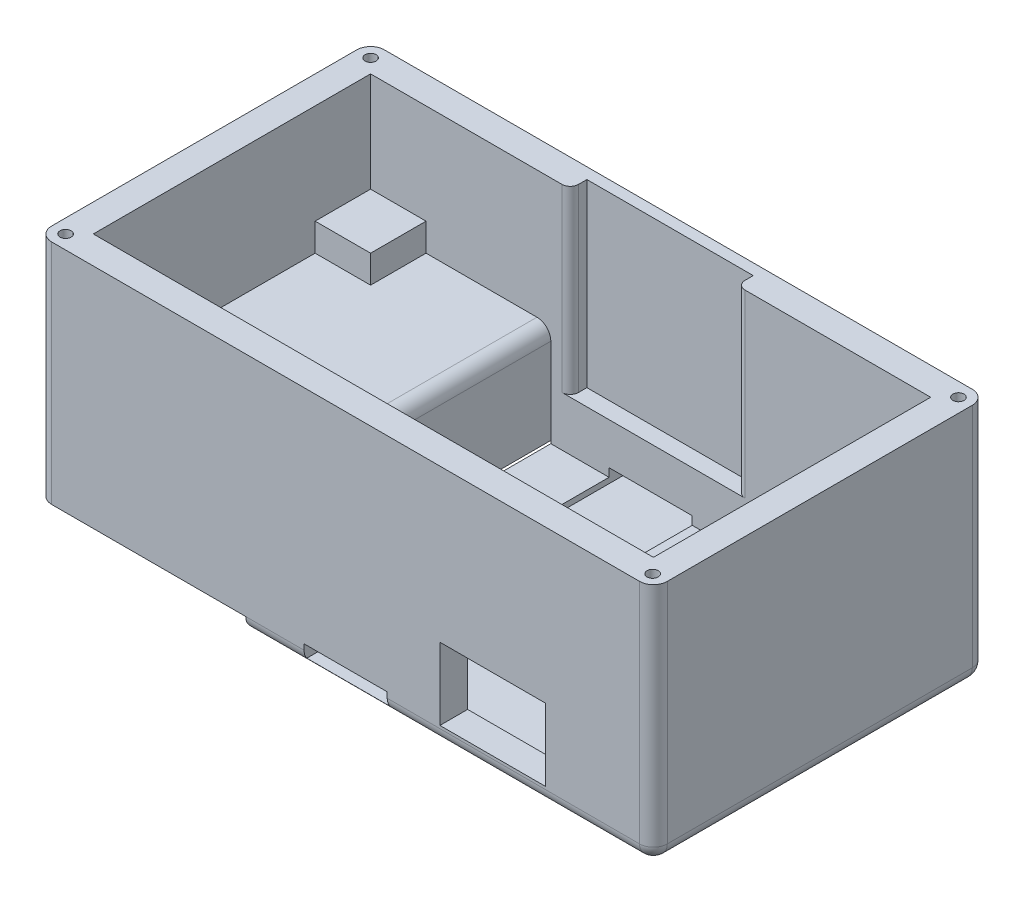
SolidWorks part; units mm, degrees
ref_plane "Front Plane" through (0, 0, 0) normal (0, 0, 1) x (1, 0, 0)
ref_plane "Top Plane" through (0, 0, 0) normal (0, 1, 0) x (1, 0, 0)
ref_plane "Right Plane" through (0, 0, 0) normal (1, 0, 0) x (0, 0, -1)
sketch "Sketch1" plane through (0, 0, 0) normal (0, 1, 0) x (1, 0, 0)
  line L1 (0, 0) -> (111, 0)
  line L2 (0, 0) -> (0, 60)
  line L3 (0, 60) -> (111, 60)
  line L4 (111, 0) -> (111, 60)
  dimension "D1" = 111
  dimension "D2" = 60
extrude "Boss-Extrude1" add sketch "Sketch1" along normal blind 43.5
sketch "Sketch2" plane through (0, 43.5, 0) normal (0, 1, 0) x (1, 0, 0)
  line L0 (55.5, 60) -> (55.5, 0) construction
  line L1 (111, 60) -> (0, 60) construction
  line L2 (0, 0) -> (111, 0) construction
  line L3 (0, 30) -> (111, 30) construction
  line L4 (0, 60) -> (0, 0) construction
  line L5 (111, 0) -> (111, 60) construction
  line L7 (5, 5) -> (106, 5)
  line L8 (5, 5) -> (5, 55)
  line L9 (5, 55) -> (106, 55)
  line L10 (106, 5) -> (106, 55)
  dimension "D1" = 5
  dimension "D2" = 5
  dimension "D3" = 5
  dimension "D4" = 5
  dimension "D5" = 50
  dimension "D6" = 101
extrude "Cut-Extrude1" cut sketch "Sketch2" against normal blind 18
sketch "Sketch3" plane through (0, 43.5, 0) normal (0, 1, 0) x (1, 0, 0)
  line L0 (5, 45) -> (15, 45)
  line L1 (5, 55) -> (5, 5) construction
  line L2 (15, 45) -> (15, 55)
  line L3 (106, 55) -> (5, 55) construction
  line L4 (15, 55) -> (96, 55)
  line L5 (96, 55) -> (96, 45)
  line L6 (96, 45) -> (106, 45)
  line L7 (106, 5) -> (106, 55) construction
  line L8 (106, 45) -> (106, 15)
  line L9 (106, 5) -> (106, 55) construction
  line L10 (106, 15) -> (96, 15)
  line L11 (96, 15) -> (96, 5)
  line L12 (5, 5) -> (106, 5) construction
  line L13 (96, 5) -> (15, 5)
  line L14 (15, 5) -> (15, 15)
  line L15 (15, 15) -> (5, 15)
  line L16 (5, 55) -> (5, 5) construction
  line L17 (5, 15) -> (5, 45)
  dimension "D1" = 10
  dimension "D2" = 10
  dimension "D3" = 10
  dimension "D4" = 10
  dimension "D5" = 10
  dimension "D6" = 10
  dimension "D7" = 10
  dimension "D8" = 10
extrude "Cut-Extrude3" cut sketch "Sketch3" against normal blind 23
sketch "Sketch5" plane through (0, 0, 0) normal (0, -1, 0) x (1, 0, 0)
  line L6 (0, 0) -> (111, 0) construction
  line L14 (111, 0) -> (111, -60) construction
  line L15 (106, -55) -> (37.5, -55)
  line L16 (106, -55) -> (106, -5)
  line L17 (106, -5) -> (37.5, -5)
  line L18 (37.5, -55) -> (37.5, -5)
  line L19 (111, -60) -> (0, -60) construction
  dimension "D6" = 5
  dimension "D7" = 5
  dimension "D8" = 5
extrude "Cut-Extrude5" cut sketch "Sketch5" against normal blind 18.5 from offset 2 offset against normal yes
sketch "Sketch6" plane through (0, 0, 0) normal (0, -1, 0) x (1, 0, 0)
  line L0 (0, 0) -> (111, 0) construction
  line L1 (0, -60) -> (37.5, -60)
  line L2 (0, -60) -> (0, 0)
  line L3 (0, 0) -> (37.5, 0)
  line L4 (37.5, -60) -> (37.5, 0)
  dimension "D1" = 60
  dimension "D2" = 37.5
extrude "Cut-Extrude6" cut sketch "Sketch6" against normal blind 2.5
sketch "Sketch7" plane through (0, 2.5, 0) normal (0, -1, 0) x (-1, 0, 0)
  line L0 (-37.5, 0) -> (0, 0) construction
  line L1 (0, 0) -> (0, 60) construction
  line L2 (0, 60) -> (-37.5, 60) construction
  line L3 (-37.5, 60) -> (-37.5, 0) construction
  line L4 (-37.5, 60) -> (-37.5, 55) construction
  circle A0 centre (-2.5, 57.5) radius 1
  circle A1 centre (-35, 57.5) radius 1
  circle A2 centre (-35, 2.5) radius 1
  circle A3 centre (-2.5, 2.5) radius 1
  dimension "D1" = 2
  dimension "D2" = 2
  dimension "D3" = 2
  dimension "D4" = 2
  dimension "D5" = 2.5
  dimension "D6" = 2.5
  dimension "D7" = 2.5
  dimension "D8" = 2.5
  dimension "D9" = 2.5
  dimension "D10" = 2.5
  dimension "D11" = 2.5
  dimension "D12" = 2.5
extrude "Cut-Extrude7" cut sketch "Sketch7" against normal blind 4
sketch "Sketch8" plane through (0, 43.5, 0) normal (0, 1, 0) x (1, 0, 0)
  line L0 (111, 60) -> (0, 60) construction
  line L1 (111, 0) -> (111, 60) construction
  line L2 (0, 60) -> (0, 0) construction
  line L3 (0, 0) -> (111, 0) construction
  circle A0 centre (2.5, 57.5) radius 1
  circle A1 centre (108.5, 57.5) radius 1
  circle A2 centre (108.5, 2.3604) radius 1
  circle A3 centre (2.5, 2.5) radius 1
  dimension "D8" = 2
  dimension "D9" = 2
  dimension "D10" = 2
  dimension "D12" = 2
  dimension "D1" = 2.5
  dimension "D2" = 2.5
  dimension "D3" = 2.5
  dimension "D4" = 2.5
  dimension "D5" = 2.5
  dimension "D6" = 2.5
  dimension "D7" = 2.5
  dimension "D11" = 2.5
extrude "Cut-Extrude8" cut sketch "Sketch8" against normal blind 4
sketch "Sketch9" plane through (0, 0, 0) normal (0, 0, 1) x (1, 0, 0)
  line L0 (37.5, 2.5) -> (37.5, 0) construction
  line L1 (72.5, 3) -> (91.5, 3)
  line L2 (72.5, 3) -> (72.5, 16)
  line L3 (72.5, 16) -> (91.5, 16)
  line L4 (91.5, 3) -> (91.5, 16)
  line L5 (37.5, 0) -> (111, 0) construction
  line L6 (0, 43.5) -> (111, 43.5) construction
  dimension "D1" = 13
  dimension "D2" = 19
  dimension "D3" = 3
  dimension "D4" = 27.5
  dimension "D5" = 35
extrude "Cut-Extrude9" cut sketch "Sketch9" against normal blind 10
sketch "Sketch12" plane through (0, 43.5, 0) normal (0, 1, 0) x (1, 0, 0)
  line L0 (106, 55) -> (5, 55) construction
  line L1 (71, 55) -> (41, 55)
  line L2 (71, 55) -> (71, 58)
  line L3 (71, 58) -> (41, 58)
  line L4 (41, 55) -> (41, 58)
  line L5 (111, 0) -> (111, 60) construction
  dimension "D1" = 40
  dimension "D2" = 70
  dimension "D3" = 3
  dimension "D4" = 30
extrude "Cut-Extrude12" cut sketch "Sketch12" against normal blind 32.5
fillet "Fillet2" radius 2.5 1 edges at (0, 23, 0)
fillet "Fillet3" radius 2.5 1 edges at (111, 21.75, 0)
fillet "Fillet4" radius 2.5 1 edges at (0, 23, -60)
fillet "Fillet5" radius 2.5 1 edges at (111, 21.75, -60)
fillet "Fillet6" radius 2.5 5 edges at (73, 0, -60) (110.2678, 0, -59.2678) (111, 0, -30) (110.2678, 0, -0.7322) (73, 0, 0)
sketch "Sketch13" plane through (0, 2.5, 0) normal (0, -1, 0) x (1, 0, 0)
  line L0 (37.5, -57.5) -> (37.5, -2.5) construction
  line L1 (5, -2) -> (32.5, -2)
  line L2 (5, -2) -> (5, -58)
  line L3 (5, -58) -> (32.5, -58)
  line L4 (32.5, -2) -> (32.5, -58)
  line L5 (0, -2.5) -> (0, -57.5) construction
  line L6 (2.5, -60) -> (37.5, -60) construction
  line L7 (37.5, 0) -> (2.5, 0) construction
  dimension "D1" = 5
  dimension "D2" = 27.5
  dimension "D3" = 5
  dimension "D4" = 56
  dimension "D5" = 2
  dimension "D6" = 2
extrude "Cut-Extrude13" cut sketch "Sketch13" against normal blind 17
sketch "Sketch14" plane through (0, 19.5, 0) normal (0, -1, 0) x (1, 0, 0)
  line L0 (5, -2) -> (5, -58) construction
  line L13 (32, -6.1341) -> (17, -6.1341)
  line L14 (32, -6.1341) -> (32, -16.1341)
  line L15 (32, -16.1341) -> (17, -16.1341)
  line L16 (17, -6.1341) -> (17, -16.1341)
  dimension "D1" = 10
  dimension "D2" = 15
  dimension "D3" = 10
  dimension "D4" = 12
extrude "Cut-Extrude14" cut sketch "Sketch14" against normal through all
fillet "Fillet7" radius 1.5 1 edges at (32.5, 11, -2)
fillet "Fillet8" radius 1.5 1 edges at (5, 11, -2)
fillet "Fillet9" radius 1.5 1 edges at (32.5, 11, -58)
fillet "Fillet10" radius 1.5 1 edges at (5, 11, -58)
fillet "Fillet11" radius 2.5 1 edges at (37.5, 20.5, -30)
fillet "Fillet12" radius 1.5 2 edges at (41, 27.25, -55) (71, 27.25, -55)
sketch "Sketch15" plane through (37.5, 0, 0) normal (1, 0, 0) x (0, 0, -1)
  line L1 (7.6101, 15.9077) -> (29.7175, 15.9077)
  line L2 (7.6101, 15.9077) -> (7.6101, 11.0681)
  line L3 (7.6101, 11.0681) -> (29.7175, 11.0681)
  line L4 (29.7175, 15.9077) -> (29.7175, 11.0681)
extrude "Cut-Extrude15" cut sketch "Sketch15" against normal blind 10
sketch "Sketch16" plane through (0, 0, 0) normal (0, 0, 1) x (1, 0, 0)
  line L0 (108.5, 0) -> (37.5, 0) construction
  line L1 (48, 1) -> (63, 1)
  line L2 (48, 1) -> (48, 3.5)
  line L3 (48, 3.5) -> (63, 3.5)
  line L4 (63, 1) -> (63, 3.5)
  line L5 (55.5, 43.5) -> (55.5, 0) construction
  line L6 (2.5, 43.5) -> (108.5, 43.5) construction
  dimension "D1" = 15
  dimension "D2" = 15
  dimension "D3" = 1
  dimension "D4" = 2.5
  dimension "D5" = 7.5
extrude "Cut-Extrude16" cut sketch "Sketch16" against normal through all
equation "\"`\"=1.26241"
